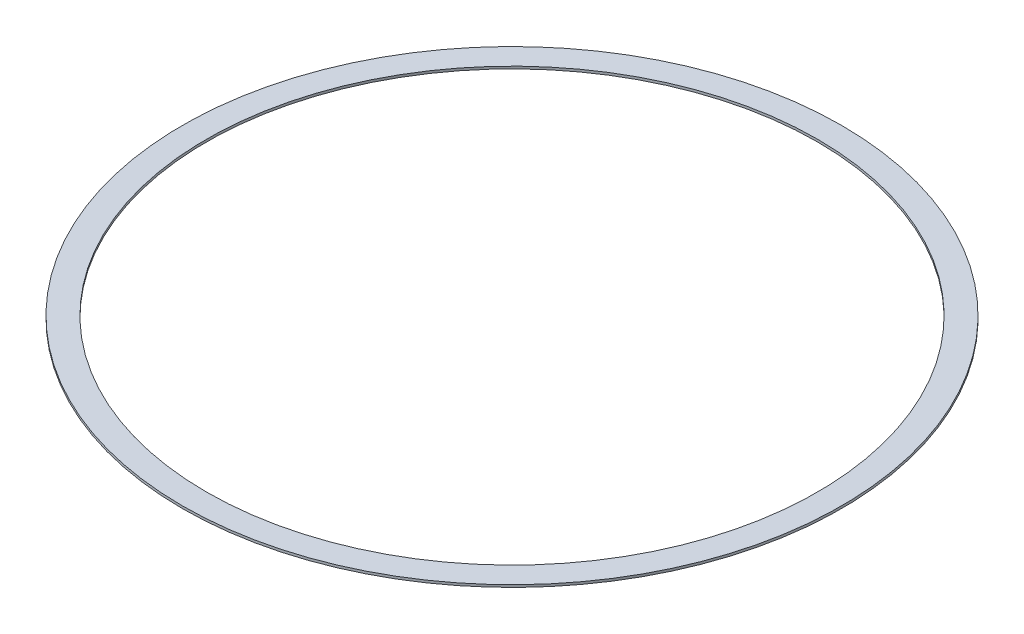
SolidWorks part; units mm, degrees
ref_plane "前视基准面" through (0, 0, 0) normal (0, 0, 1) x (1, 0, 0)
ref_plane "上视基准面" through (0, 0, 0) normal (0, 1, 0) x (1, 0, 0)
ref_plane "右视基准面" through (0, 0, 0) normal (1, 0, 0) x (0, 0, -1)
sketch "草图2" plane through (0, 0, 0) normal (0, 1, 0) x (1, 0, 0)
  circle A0 centre (0, 0) radius 274.63
  circle A1 centre (0, 0) radius 254.63
  dimension "D1" = 509.2599
  dimension "D2" = 20
extrude "凸台-拉伸1" add sketch "草图2" along normal blind 2
